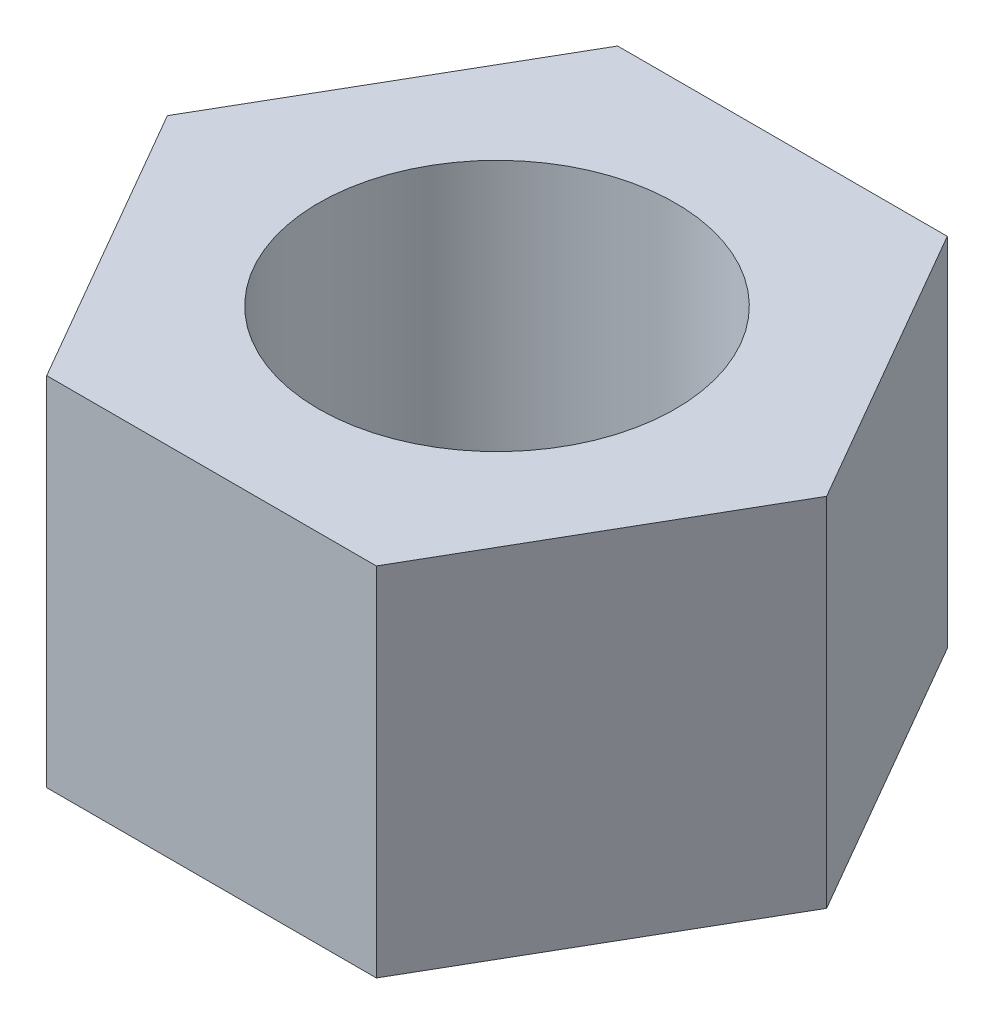
SolidWorks part; units mm, degrees
ref_plane "Front Plane" through (0, 0, 0) normal (0, 0, 1) x (1, 0, 0)
ref_plane "Top Plane" through (0, 0, 0) normal (0, 1, 0) x (1, 0, 0)
ref_plane "Right Plane" through (0, 0, 0) normal (1, 0, 0) x (0, 0, -1)
sketch "Sketch2" plane through (0, 0, 0) normal (0, 1, 0) x (1, 0, 0)
  line L1 (4.6188, 0) -> (2.3094, 4)
  line L2 (2.3094, 4) -> (-2.3094, 4)
  line L3 (-2.3094, 4) -> (-4.6188, 0)
  line L4 (-4.6188, 0) -> (-2.3094, -4)
  line L5 (-2.3094, -4) -> (2.3094, -4)
  line L6 (2.3094, -4) -> (4.6188, 0)
  circle A0 centre (0, 0) radius 4 construction
  dimension "D1" = 8
extrude "Boss-Extrude1" add sketch "Sketch2" along normal blind 5
sketch "Sketch3" plane through (0, 5, 0) normal (0, 1, 0) x (1, 0, 0)
  circle A0 centre (0, 0) radius 2.5
  dimension "D1" = 5
extrude "Cut-Extrude1" cut sketch "Sketch3" against normal through all
cosmetic thread "Cosmetic Thread1" [suppressed] parameters "D2"=6
cosmetic thread "Cosmetic Thread2" [suppressed] parameters "D2"=6
